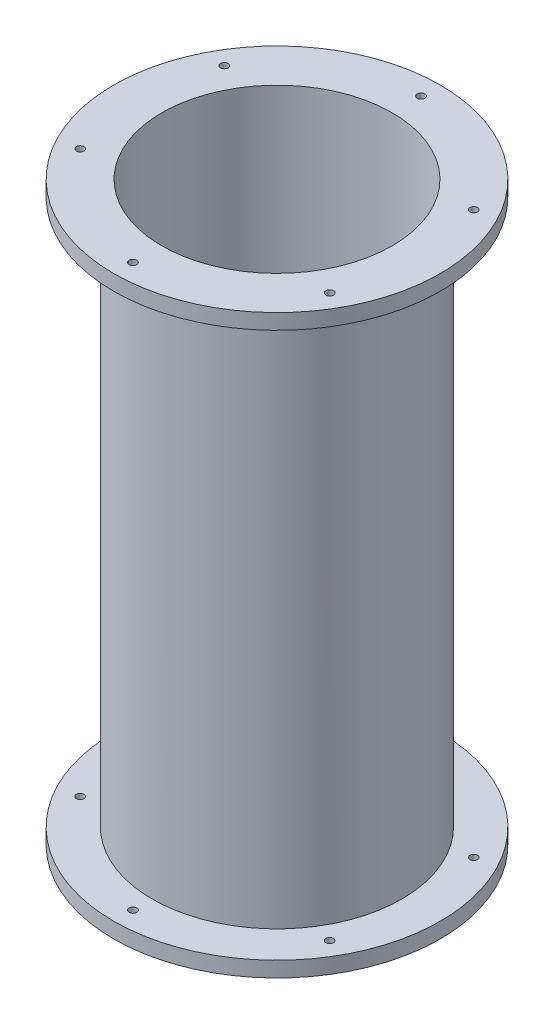
SolidWorks part; units mm, degrees
ref_plane "前视基准面" through (0, 0, 0) normal (0, 0, 1) x (1, 0, 0)
ref_plane "上视基准面" through (0, 0, 0) normal (0, 1, 0) x (1, 0, 0)
ref_plane "右视基准面" through (0, 0, 0) normal (1, 0, 0) x (0, 0, -1)
sketch "草图1" plane through (0, 0, 0) normal (0, 1, 0) x (1, 0, 0)
  circle A0 centre (0, 0) radius 65
extrude "拉伸-薄壁1" add sketch "草图1" along normal blind 300 thin thin type one direction reverse wall 5
sketch "草图2" plane through (0, 300, 0) normal (0, 1, 0) x (1, 0, 0)
  circle A0 centre (0, 0) radius 85
  circle A1 centre (0, 0) radius 65
extrude "凸台-拉伸1" add sketch "草图2" against normal blind 8
sketch "草图3" plane through (0, 300, 0) normal (0, 1, 0) x (1, 0, 0)
  line L0 (0, 0) -> (0, 85) construction
  line L1 (0, 85) -> (0, 75) construction
  circle A0 centre (0, 0) radius 85 construction
  circle A1 centre (0, 75) radius 2
  circle A2 centre (64.9519, 37.5) radius 2
  circle A3 centre (64.9519, -37.5) radius 2
  circle A4 centre (0, -75) radius 2
  circle A5 centre (-64.9519, -37.5) radius 2
  circle A6 centre (-64.9519, 37.5) radius 2
  point P21 (0, 0)
  dimension "D1" = 6
extrude "切除-拉伸1" cut sketch "草图3" against normal through all contours A2 | A3 | A1 | A4 | A5 | A6
sketch "草图4" plane through (0, 0, 0) normal (0, -1, 0) x (1, 0, 0)
  circle A0 centre (0, 0) radius 85
  circle A1 centre (0, 0) radius 65
extrude "凸台-拉伸2" add sketch "草图4" against normal blind 8
sketch "草图5" plane through (0, 0, 0) normal (0, -1, 0) x (1, 0, 0)
  line L0 (0, 0) -> (0, 85) construction
  line L1 (0, 85) -> (0, 75) construction
  circle A0 centre (0, 0) radius 85 construction
  circle A1 centre (0, 75) radius 2
  circle A2 centre (64.9519, 37.5) radius 2
  circle A3 centre (64.9519, -37.5) radius 2
  circle A4 centre (0, -75) radius 2
  circle A5 centre (-64.9519, -37.5) radius 2
  circle A6 centre (-64.9519, 37.5) radius 2
  point P20 (0, 0)
  dimension "D1" = 6
extrude "切除-拉伸2" cut sketch "草图5" against normal through all and the other way through all contours A2 | A3 | A4 | A1 | A5 | A6
